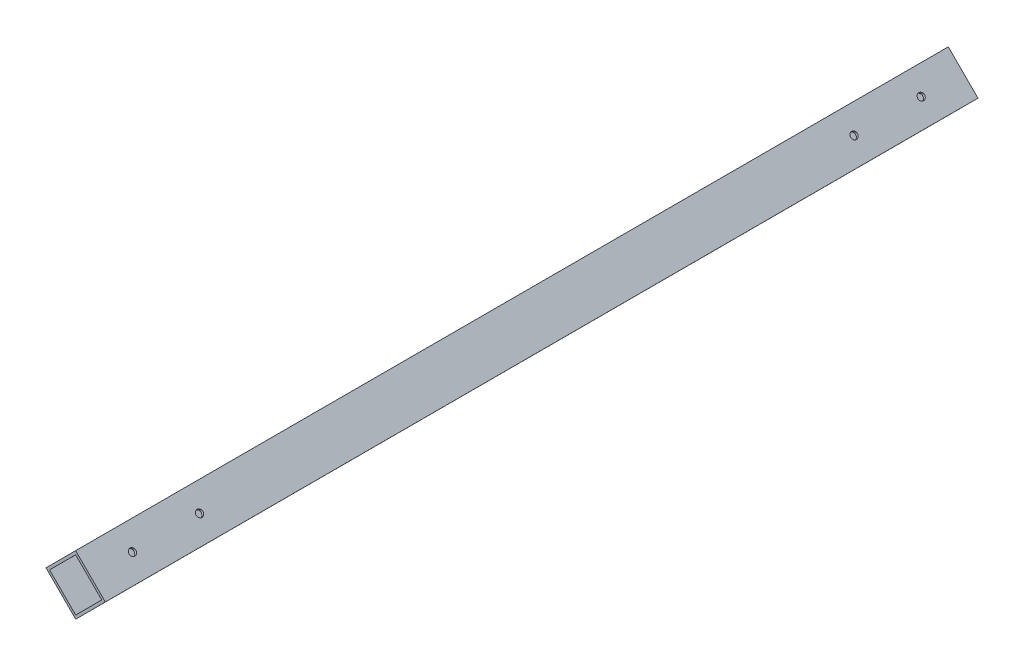
SolidWorks part; units mm, degrees
material "可鍛鑄鐵"
ref_plane "前基準面" through (0, 0, 0) normal (0, 0, 1) x (1, 0, 0)
ref_plane "上基準面" through (0, 0, 0) normal (0, 1, 0) x (1, 0, 0)
ref_plane "右基準面" through (0, 0, 0) normal (1, 0, 0) x (0, 0, -1)
sketch "草圖1" plane through (0, 0, 0) normal (0, 0, 1) x (1, 0, 0)
  line L0 (0, 0) -> (17.6938, -17.6615)
  line L1 (0, 0) -> (-17.6615, -17.6938)
  line L2 (17.6938, -17.6615) -> (0.0323, -35.3553)
  line L3 (-17.6615, -17.6938) -> (0.0323, -35.3553)
  line L4 (0.0019, -2.1213) -> (-15.5402, -17.6919)
  line L5 (0.0019, -2.1213) -> (15.5725, -17.6635)
  line L6 (-15.5402, -17.6919) -> (0.0303, -33.234)
  line L7 (15.5725, -17.6635) -> (0.0303, -33.234)
  point P0 (8.8469, -8.8308)
  dimension "D1" = 25
  dimension "D2" = 25
  dimension "D3" = 1.5
  dimension "D4" = 1.5
  dimension "D5" = 1.5
  dimension "D6" = 1.5
extrude "填料-伸長1" add sketch "草圖1" along normal blind 520
sketch "草圖2" plane through (0, 0, 0) normal (0.7065, 0.7078, 0) x (0.7078, -0.7065, 0)
  line L0 (25, -520) -> (0, -520) construction
  line L1 (25, -520) -> (25, 0) construction
  line L2 (25, 0) -> (0, 0) construction
  line L3 (0, -520) -> (0, 0) construction
  circle A0 centre (12.5, -495) radius 2
  circle A1 centre (12.5, -455) radius 2
  circle A2 centre (12.5, -25) radius 2
  circle A3 centre (12.5, -65) radius 2
  dimension "D1" = 4
  dimension "D2" = 4
  dimension "D4" = 25
  dimension "D6" = 4
  dimension "D7" = 4
  dimension "D8" = 40
  dimension "D9" = 25
  dimension "D10" = 12.5
  dimension "D3" = 40
  dimension "D5" = 12.5
extrude "除料-伸長1" cut sketch "草圖2" against normal through all contours A1 | A0 | A2 | A3
